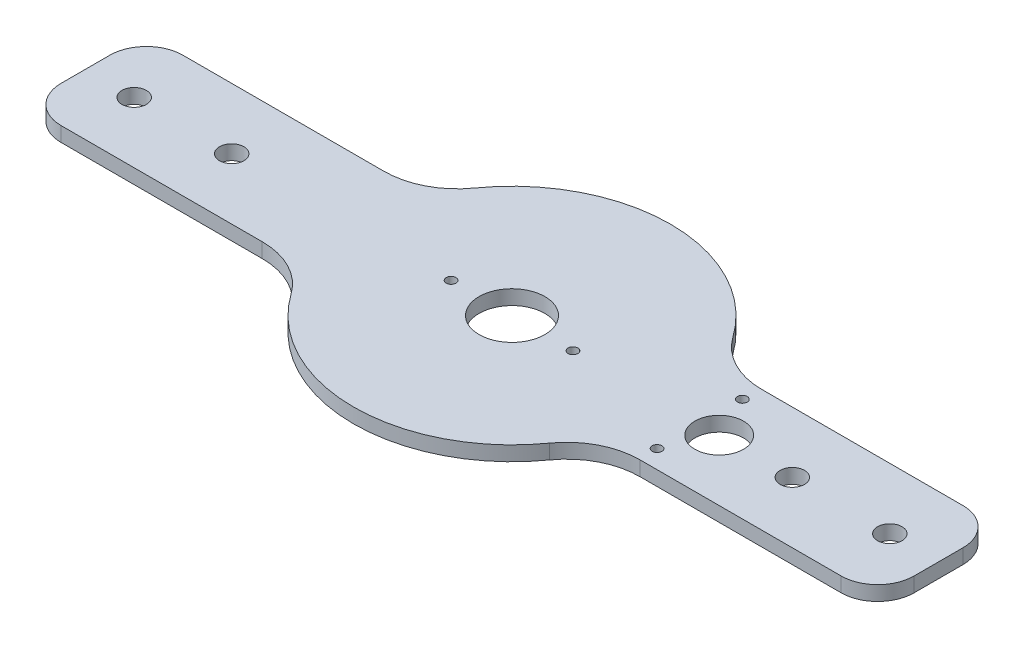
SolidWorks part; units mm, degrees
ref_plane "Plan de face" through (0, 0, 0) normal (0, 0, 1) x (1, 0, 0)
ref_plane "Plan de dessus" through (0, 0, 0) normal (0, 1, 0) x (1, 0, 0)
ref_plane "Plan de droite" through (0, 0, 0) normal (1, 0, 0) x (0, 0, -1)
sketch "Esquisse1" plane through (0, 0, 0) normal (0, 1, 0) x (1, 0, 0)
  line L0 (0, 0) -> (184.4342, 0) construction
  line L1 (0, 0) -> (-225.5183, 0) construction
  line L2 (-160, 25) -> (-77.4597, 25)
  line L3 (-175, 10) -> (-175, -10)
  line L4 (175, 10) -> (175, -10)
  line L5 (-160, -25) -> (-77.4597, -25)
  line L6 (-175, 25) -> (175, -25) construction
  line L7 (175, 25) -> (-175, -25) construction
  line L8 (77.4597, 25) -> (160, 25)
  line L9 (77.4597, -25) -> (160, -25)
  line L10 (0, 0) -> (0, -98.9171) construction
  line L11 (77, 0) -> (77, 17.5) construction
  circle A0 centre (0, 0) radius 13.5
  arc A1 (52.9987, 37.6316) -> (-52.9987, 37.6316) centre (0, 0) ccw
  arc A2 (-52.9987, -37.6316) -> (52.9987, -37.6316) centre (0, 0) ccw
  arc A3 (-52.9987, 37.6316) -> (-77.4597, 25) centre (-77.4597, 55) cw
  arc A4 (-52.9987, -37.6316) -> (-77.4597, -25) centre (-77.4597, -55) ccw
  arc A5 (77.4597, -25) -> (52.9987, -37.6316) centre (77.4597, -55) ccw
  arc A6 (77.4597, 25) -> (52.9987, 37.6316) centre (77.4597, 55) cw
  arc A7 (175, 10) -> (160, 25) centre (160, 10) ccw
  arc A8 (175, -10) -> (160, -25) centre (160, -10) cw
  arc A9 (-160, -25) -> (-175, -10) centre (-160, -10) cw
  arc A10 (-160, 25) -> (-175, 10) centre (-160, 10) ccw
  circle A11 centre (-115, 0) radius 5
  circle A12 centre (-155, 0) radius 5
  circle A13 centre (155, 0) radius 5
  circle A14 centre (115, 0) radius 5
  circle A15 centre (85, 0) radius 10
  circle A16 centre (-25, 0) radius 2
  circle A17 centre (25, 0) radius 2
  circle A18 centre (77, 17.5) radius 2
  circle A19 centre (77, -17.5) radius 2
  point P19 (60, -25)
  point P22 (60, 25)
  point P35 (-155, 0)
  point P36 (-115, 0)
  point P48 (-25, 0)
  point P53 (77, 0)
  dimension "D1" = 27
  dimension "D2" = 350
  dimension "D4" = 30
  dimension "D5" = 15
  dimension "D6" = 65
  dimension "D8" = 10
  dimension "D9" = 10
  dimension "D11" = 85
  dimension "D13" = 4
  dimension "D17" = 4
  dimension "D3" = 50
  dimension "D7" = 40
  dimension "D10" = 20
  dimension "D12" = 25
  dimension "D14" = 40
  dimension "D15" = 8
  dimension "D16" = 17.5
extrude "Boss.-Extru.1" add sketch "Esquisse1" along normal blind 6
